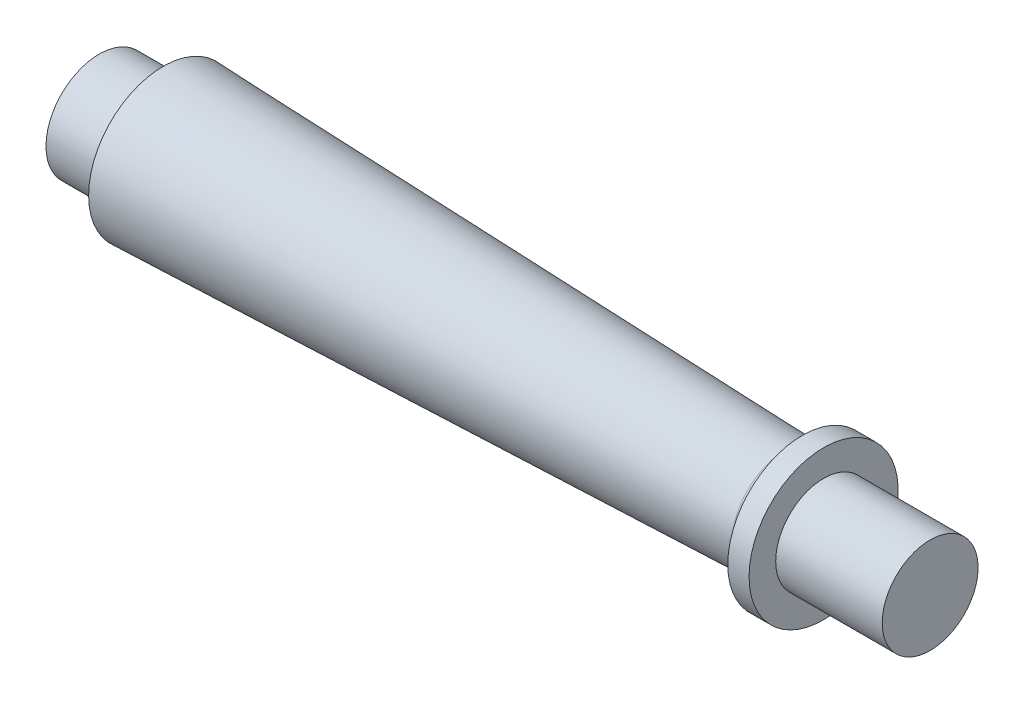
SolidWorks part; units mm, degrees
ref_plane "Front Plane" through (0, 0, 0) normal (0, 0, 1) x (1, 0, 0)
ref_plane "Top Plane" through (0, 0, 0) normal (0, 1, 0) x (1, 0, 0)
ref_plane "Right Plane" through (0, 0, 0) normal (1, 0, 0) x (0, 0, -1)
sketch "Sketch1" plane through (0, 0, 0) normal (0, 0, 1) x (1, 0, 0)
  line L0 (0, 0) -> (78, 0)
  line L1 (78, 0) -> (78, 4.5)
  line L2 (78, 4.5) -> (68, 4.5)
  line L3 (68, 4.5) -> (68, 7)
  line L4 (68, 7) -> (66, 7)
  line L5 (66, 7) -> (66, 5)
  line L6 (66, 5) -> (6, 7)
  line L7 (6, 7) -> (6, 5)
  line L8 (6, 5) -> (0, 5)
  line L9 (0, 5) -> (0, 0)
  dimension "D1" = 4.5
  dimension "D2" = 2
  dimension "D3" = 5
  dimension "D4" = 5
  dimension "D5" = 7
  dimension "D6" = 6
  dimension "D7" = 60
  dimension "D8" = 10
  dimension "D9" = 7
revolve "Revolve1" add sketch "Sketch1" angle 360 about L0
cosmetic thread "Cosmetic Thread1" parameters "D1"=10, "D2"=6.891
cosmetic thread "Cosmetic Thread2" parameters "D1"=6, "D2"=6.619
fillet "Fillet1" radius 1.5 1 edges at (66, 0, 5)
